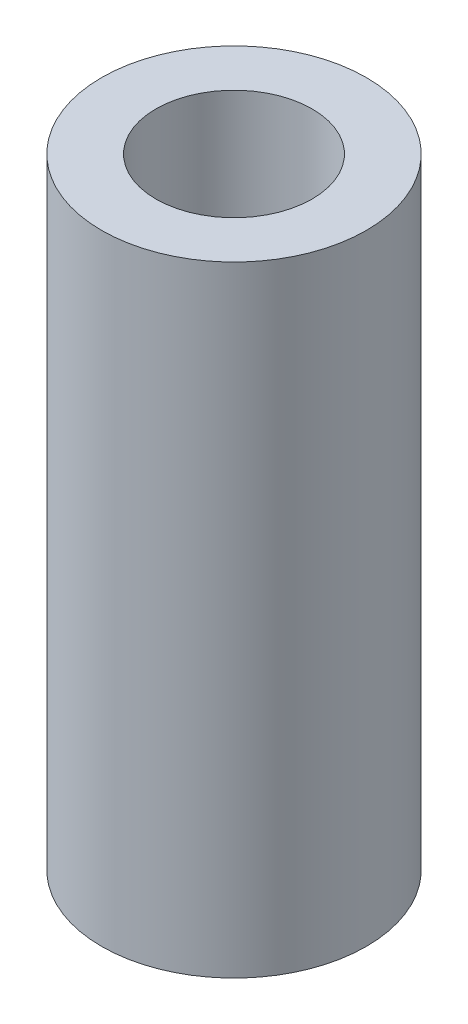
SolidWorks part; units mm, degrees
ref_plane "Front Plane" through (0, 0, 0) normal (0, 0, 1) x (1, 0, 0)
ref_plane "Top Plane" through (0, 0, 0) normal (0, 1, 0) x (1, 0, 0)
ref_plane "Right Plane" through (0, 0, 0) normal (1, 0, 0) x (0, 0, -1)
sketch "Sketch1" plane through (0, 0, 0) normal (0, 1, 0) x (1, 0, 0)
  circle A0 centre (0, 0) radius 3.6
  circle A1 centre (0, 0) radius 6.1
  dimension "D1" = 7.2
  dimension "D2" = 12.2
extrude "Boss-Extrude1" add sketch "Sketch1" along normal blind 28.575
